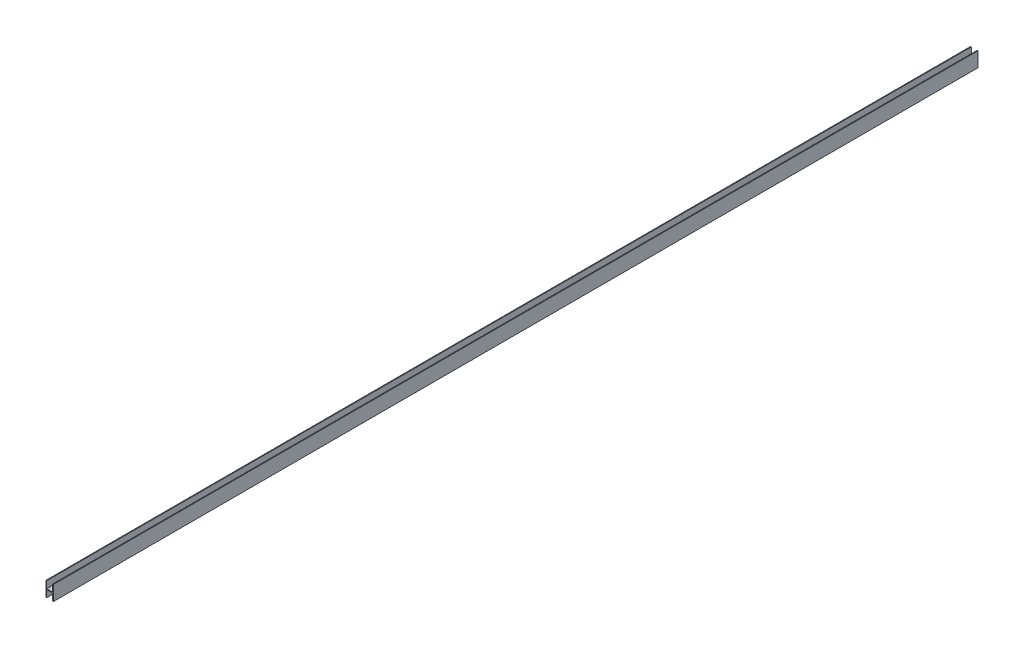
SolidWorks part; units mm, degrees
ref_plane "前视基准面" through (0, 0, 0) normal (0, 0, 1) x (1, 0, 0)
ref_plane "上视基准面" through (0, 0, 0) normal (0, 1, 0) x (1, 0, 0)
ref_plane "右视基准面" through (0, 0, 0) normal (1, 0, 0) x (0, 0, -1)
sketch "草图1" plane through (0, 0, 0) normal (0, 0, 1) x (1, 0, 0)
  line L1 (-5, -10) -> (5, -10)
  line L2 (-5, -10) -> (-5, 10)
  line L3 (-5, 10) -> (5, 10)
  line L4 (5, -10) -> (5, 10)
  line L5 (-5, -10) -> (5, 10) construction
  line L6 (-5, 10) -> (5, -10) construction
  point P0 (0, 0)
  dimension "D1" = 20
  dimension "D2" = 10
extrude "凸台-拉伸1" add sketch "草图1" along normal up to vertex (1251 mm away)
sketch "草图2" plane through (0, 0, 0) normal (0, 0, -1) x (-1, 0, 0)
  line L0 (-5, 10) -> (5, 10) construction
  line L1 (-4, 19.5) -> (4, 19.5)
  line L2 (-4, 19.5) -> (-4, 0.5)
  line L3 (-4, 0.5) -> (4, 0.5)
  line L4 (4, 19.5) -> (4, 0.5)
  line L5 (-4, 19.5) -> (4, 0.5) construction
  line L6 (-4, 0.5) -> (4, 19.5) construction
  line L7 (5, -10) -> (-5, -10) construction
  line L8 (-4, -0.5) -> (4, -0.5)
  line L9 (-4, -0.5) -> (-4, -19.5)
  line L10 (-4, -19.5) -> (4, -19.5)
  line L11 (4, -0.5) -> (4, -19.5)
  line L12 (-4, -0.5) -> (4, -19.5) construction
  line L13 (-4, -19.5) -> (4, -0.5) construction
  point P0 (0, 10)
  point P7 (0, -10)
  dimension "D1" = 8
  dimension "D2" = 8
  dimension "D3" = 0.5
  dimension "D4" = 0.5
extrude "切除-拉伸1" cut sketch "草图2" against normal blind 2503
